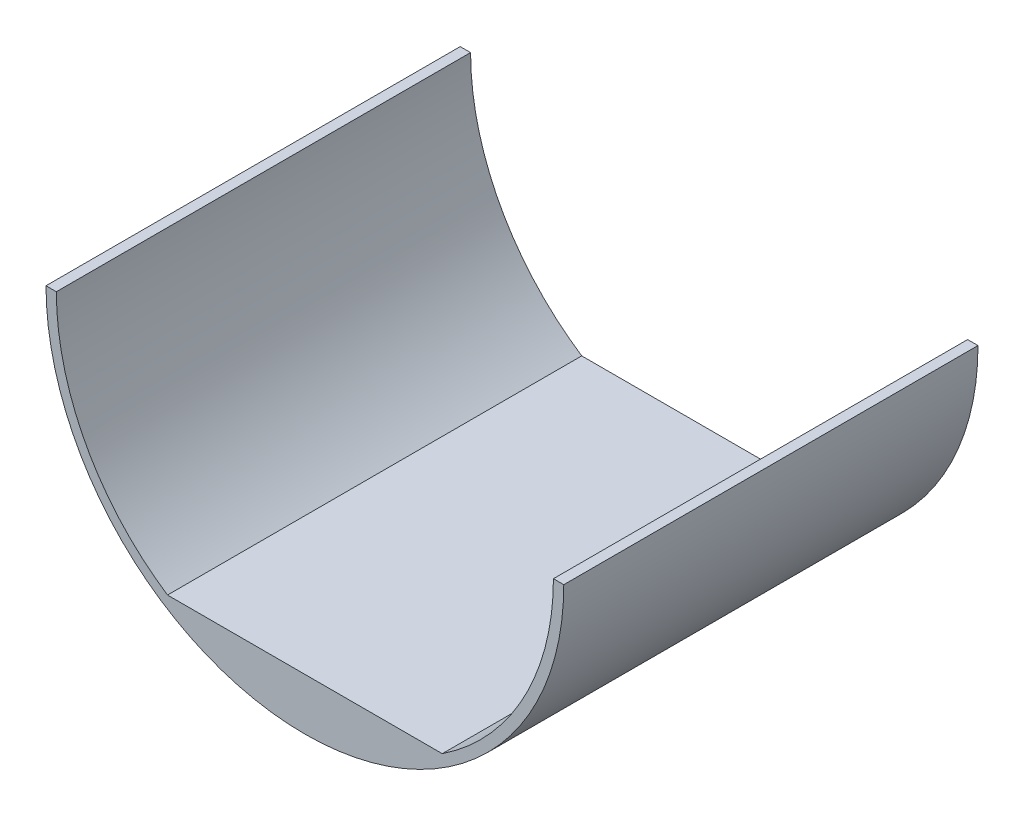
SolidWorks part; units mm, degrees
ref_plane "Front Plane" through (0, 0, 0) normal (0, 0, 1) x (1, 0, 0)
ref_plane "Top Plane" through (0, 0, 0) normal (0, 1, 0) x (1, 0, 0)
ref_plane "Right Plane" through (0, 0, 0) normal (1, 0, 0) x (0, 0, -1)
sketch "Sketch3" plane through (0, 0, 0) normal (0, 0, 1) x (1, 0, 0)
  line L0 (0, 0) -> (63.5, 0)
  line L1 (0, 0) -> (-63.5, 0)
  line L2 (-33.6969, -50.8) -> (33.6969, -50.8)
  arc A0 (-63.5, 0) -> (63.5, 0) centre (0, 0) ccw
  arc A1 (-60.96, 0) -> (60.96, 0) centre (0, 0) ccw
  dimension "D1" = 127
  dimension "D2" = 121.92
  dimension "D3" = 50.8
extrude "Boss-Extrude3" add sketch "Sketch3" along normal blind 101.6 contours A1 L1 A0 L0 | L2 A1
